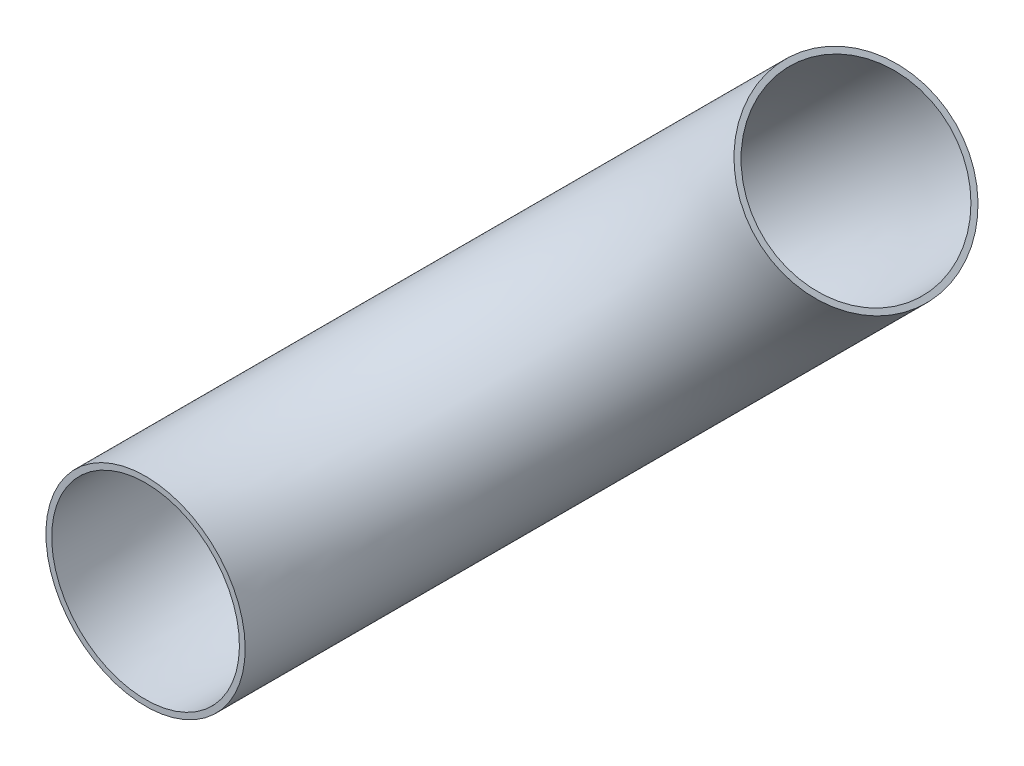
SolidWorks part; units mm, degrees
ref_plane "Front" through (0, 0, 0) normal (0, 0, 1) x (1, 0, 0)
ref_plane "Top" through (0, 0, 0) normal (0, 1, 0) x (1, 0, 0)
ref_plane "Side" through (0, 0, 0) normal (1, 0, 0) x (0, 0, -1)
sketch "PipeSketch" plane through (0, 0, 0) normal (0, 0, 1) x (1, 0, 0)
  circle A0 centre (0, 0) radius 109.474
  circle A1 centre (0, 0) radius 103.124
  dimension "OuterDiameter" = 218.948
  dimension "InnerDiameter" = 206.248
sketch "FilterSketch" plane through (0, 0, 0) normal (0, 0, 1) x (1, 0, 0)
  circle A0 centre (0, 0) radius 152.4 construction
  dimension "NominalDiameter" = 304.8
sketch3d "3DSketch1"
  arc A0 (0, 0, 0) -> (323.2892, 323.2892, -457.2) centre (323.2892, 323.2892, 0) ccw construction
  arc A1 (0, 0, 0) -> (323.2892, 323.2892, -457.2) centre (323.2892, 323.2892, 0) ccw
  point P3 (646.5784, 0, 0)
  point P4 (646.5784, 0, 0)
sweep "Sweep1" add profiles "PipeSketch" path "3DSketch1"
